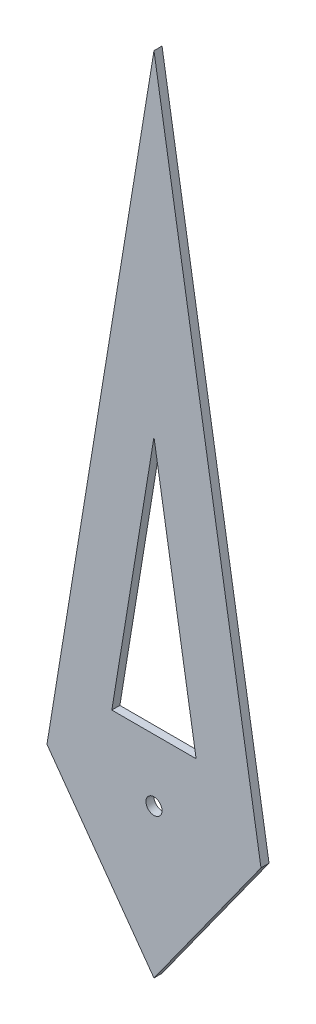
SolidWorks part; units mm, degrees
ref_plane "Front Plane" through (0, 0, 0) normal (0, 0, 1) x (1, 0, 0)
ref_plane "Top Plane" through (0, 0, 0) normal (0, 1, 0) x (1, 0, 0)
ref_plane "Right Plane" through (0, 0, 0) normal (1, 0, 0) x (0, 0, -1)
sketch "Sketch1" plane through (0, 0, 0) normal (0, 0, 1) x (1, 0, 0)
  line L0 (0, -0.3857) -> (0, 3.6774) construction
  line L1 (0, 3.6774) -> (0.6646, -0.3857)
  line L2 (0.6646, -0.3857) -> (0, -1.3102)
  line L3 (-0.6646, -0.3857) -> (0, -1.3102)
  line L4 (0, 3.6774) -> (-0.6646, -0.3857)
  line L5 (-0.2617, 0) -> (0.2617, 0)
  line L6 (0.2617, 0) -> (0, 1.6001)
  line L7 (-0.2617, 0) -> (0, 1.6001)
  point P8 (0, 0)
extrude "Boss-Extrude1" add sketch "Sketch1" along normal blind 0.05
sketch "Sketch2" plane through (0, 0, 0.05) normal (0, 0, 1) x (1, 0, 0)
  circle A0 centre (0, -0.3857) radius 0.05
  dimension "D1" = 0.1
extrude "Cut-Extrude1" cut sketch "Sketch2" against normal blind 0.05
